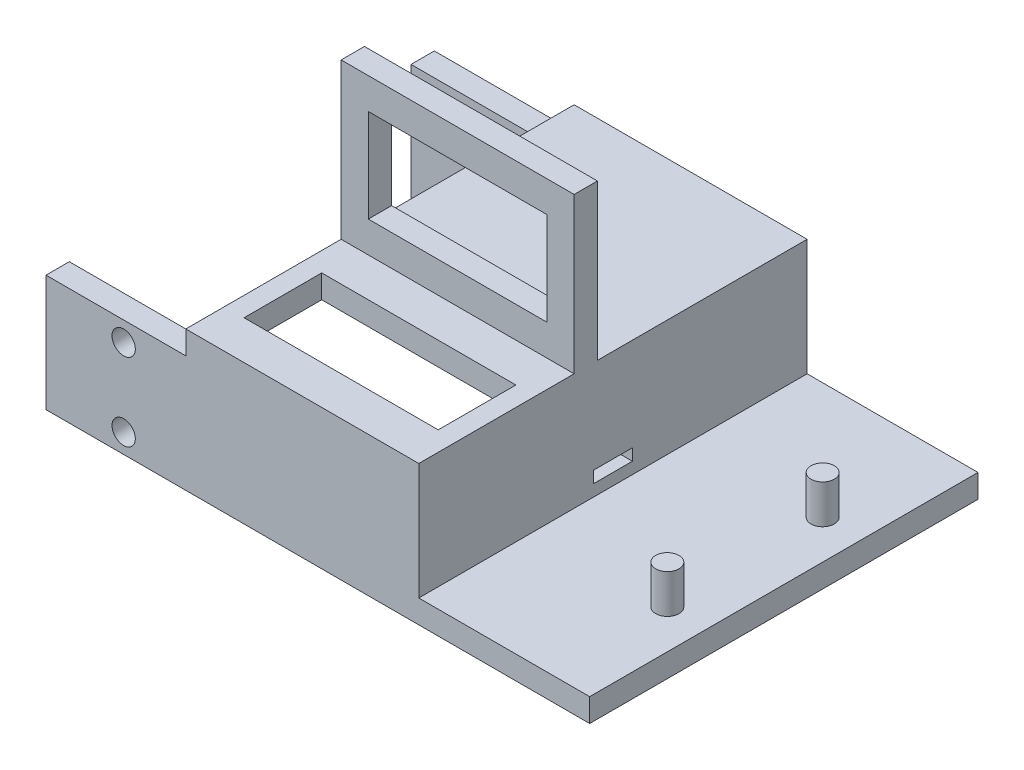
SolidWorks part; units mm, degrees
ref_plane "Front Plane" through (0, 0, 0) normal (0, 0, 1) x (1, 0, 0)
ref_plane "Top Plane" through (0, 0, 0) normal (0, 1, 0) x (1, 0, 0)
ref_plane "Right Plane" through (0, 0, 0) normal (1, 0, 0) x (0, 0, -1)
sketch "Sketch1" plane through (0, 0, 0) normal (0, 0, 1) x (1, 0, 0)
  line L0 (0, 0) -> (25, 0)
  line L1 (25, 0) -> (25, 3)
  line L2 (25, 3) -> (3, 3)
  line L3 (3, 3) -> (3, 15)
  line L4 (3, 15) -> (0, 15)
  line L5 (0, 15) -> (0, 0)
  dimension "D1" = 25
  dimension "D2" = 3
  dimension "D3" = 3
  dimension "D4" = 15
extrude "Boss-Extrude1" add sketch "Sketch1" along normal blind 50
sketch "Sketch2" plane through (0, 3, 0) normal (0, 1, 0) x (1, 0, 0)
  line L0 (3, -25) -> (25, -25) construction
  line L1 (3, -50) -> (3, 0) construction
  line L2 (25, -50) -> (25, 0) construction
  circle A0 centre (20, -15) radius 1.5
  circle A1 centre (20, -35) radius 1.5
  dimension "D1" = 3
  dimension "D2" = 5
  dimension "D3" = 10
extrude "Boss-Extrude2" add sketch "Sketch2" along normal blind 5
sketch "Sketch3" plane through (0, 0, 0) normal (-1, 0, 0) x (0, 0, 1)
  line L0 (25, 15) -> (25, 0) construction
  line L1 (50, 15) -> (0, 15) construction
  line L2 (50, 0) -> (0, 0) construction
  line L3 (0, 7.5) -> (50, 7.5) construction
  line L4 (0, 15) -> (0, 0) construction
  line L5 (50, 15) -> (50, 0) construction
  line L7 (27.5, 6) -> (22.5, 6)
  line L8 (27.5, 6) -> (27.5, 4.5)
  line L9 (27.5, 4.5) -> (22.5, 4.5)
  line L10 (22.5, 6) -> (22.5, 4.5)
  line L11 (27.5, 6) -> (22.5, 4.5) construction
  line L12 (27.5, 4.5) -> (22.5, 6) construction
  line L13 (50, 3) -> (0, 3) construction
  point P14 (25, 5.25)
  dimension "D1" = 1.5
  dimension "D3" = 1.5
  dimension "D2" = 5
extrude "Cut-Extrude1" cut sketch "Sketch3" against normal through all both and the other way through all
sketch "Sketch4" plane through (0, 0, 0) normal (0, 0, -1) x (-1, 0, 0)
  line L0 (0, 15) -> (0, 0) construction
  line L1 (0, 15) -> (45, 15)
  line L2 (0, 15) -> (0, 0)
  line L3 (0, 0) -> (45, 0)
  line L4 (45, 15) -> (45, 0)
  line L5 (0, 0) -> (-25, 0) construction
  line L6 (-3, 15) -> (0, 15) construction
  dimension "D1" = 45
extrude "Boss-Extrude3" add sketch "Sketch4" against normal blind 3
sketch "Sketch5" plane through (0, 0, 50) normal (0, 0, 1) x (1, 0, 0)
  line L1 (0, 15) -> (-45, 15)
  line L2 (0, 15) -> (0, 0)
  line L3 (0, 0) -> (-45, 0)
  line L4 (-45, 15) -> (-45, 0)
extrude "Boss-Extrude4" add sketch "Sketch5" against normal blind 3
sketch "Sketch6" plane through (0, 0, 50) normal (0, 0, 1) x (1, 0, 0)
  line L0 (-45, 7.5) -> (3, 7.5) construction
  line L1 (-45, 15) -> (-45, 0) construction
  line L2 (3, 3) -> (3, 15) construction
  circle A1 centre (-35, 12.5) radius 1.5
  circle A2 centre (-35, 2.5) radius 1.5
  dimension "D2" = 5
  dimension "D3" = 10
  dimension "D1" = 3
extrude "Cut-Extrude2" cut sketch "Sketch6" against normal through all both and the other way through all
sketch "Sketch8" plane through (0, 15, 0) normal (0, 1, 0) x (1, 0, 0)
  line L0 (3, -50) -> (-45, -50) construction
  line L1 (3, -50) -> (-27, -50)
  line L2 (3, -50) -> (3, 0)
  line L3 (3, 0) -> (-27, 0)
  line L4 (-27, -50) -> (-27, 0)
  line L5 (25, -50) -> (3, -50) construction
  line L6 (3, 0) -> (-45, 0) construction
  line L7 (3, -50) -> (3, 0) construction
  line L8 (-12, 0) -> (-12, -50) construction
  line L9 (-24.5, -35) -> (0.5, -35)
  line L10 (-24.5, -35) -> (-24.5, -45)
  line L11 (-24.5, -45) -> (0.5, -45)
  line L12 (0.5, -35) -> (0.5, -45)
  line L13 (-24.5, -35) -> (0.5, -45) construction
  line L14 (-24.5, -45) -> (0.5, -35) construction
  point P13 (-12, -40)
  dimension "D1" = 30
  dimension "D2" = 10
  dimension "D3" = 25
  dimension "D4" = 5
extrude "Boss-Extrude7" add sketch "Sketch8" along normal blind 3
sketch "Sketch9" plane through (0, 18, 0) normal (0, 1, 0) x (1, 0, 0)
  line L0 (-27, -30) -> (3, -30) construction
  line L1 (-27, 0) -> (-27, -50) construction
  line L2 (3, -50) -> (3, 0) construction
  line L3 (3, 0) -> (-27, 0) construction
  dimension "D1" = 30
sketch3d "3DSketch1"
  line L1 (-27, 18, 30) -> (3, 18, 30)
  line L2 (-27, 18, 30) -> (-27, 38, 30)
  line L3 (-27, 38, 30) -> (3, 38, 30)
  line L4 (3, 18, 30) -> (3, 38, 30)
  line L5 (-12, 38, 30) -> (-12, 18, 30) construction
  line L6 (-27, 28, 30) -> (3, 28, 30) construction
  line L8 (-23.5, 34, 30) -> (-0.5, 34, 30)
  line L9 (-23.5, 34, 30) -> (-23.5, 22, 30)
  line L10 (-23.5, 22, 30) -> (-0.5, 22, 30)
  line L11 (-0.5, 34, 30) -> (-0.5, 22, 30)
  line L12 (-23.5, 34, 30) -> (-0.5, 22, 30) construction
  line L13 (-23.5, 22, 30) -> (-0.5, 34, 30) construction
  point P11 (-12, 28, 30)
  dimension "D1" = 20
  dimension "D2" = 23
  dimension "D3" = 12
extrude "servo mount" add sketch "3DSketch1" along direction (0, 0, 1) on the side of the normal blind 3 contours L3 L4 L1 L2 | L8 L11 L10 L9
